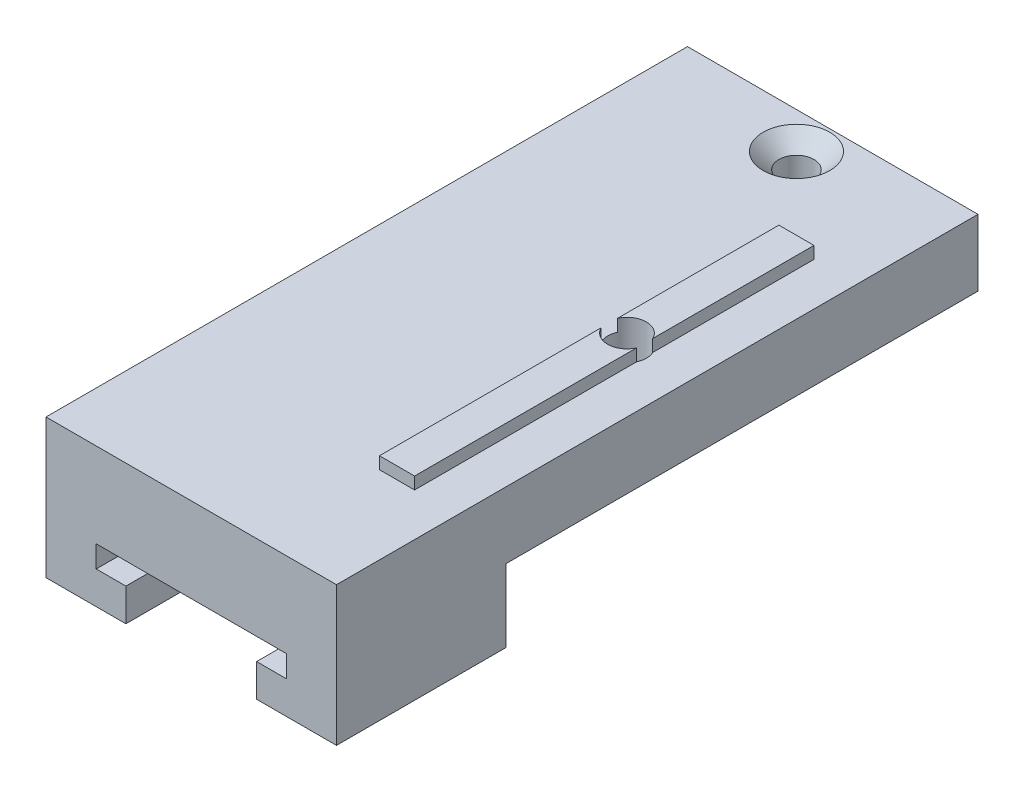
SolidWorks part; units mm, degrees
ref_plane "Front Plane" through (0, 0, 0) normal (0, 0, 1) x (1, 0, 0)
ref_plane "Top Plane" through (0, 0, 0) normal (0, 1, 0) x (1, 0, 0)
ref_plane "Right Plane" through (0, 0, 0) normal (1, 0, 0) x (0, 0, -1)
sketch "Sketch1" plane through (0, 0, 0) normal (0, 0, 1) x (1, 0, 0)
  line L0 (12, 0) -> (5.4, 0)
  line L1 (5.4, 0) -> (5.4, 2.7)
  line L2 (5.4, 2.7) -> (7.85, 2.7)
  line L3 (7.85, 2.7) -> (7.85, 4.5)
  line L5 (-5.4, 0) -> (-12, 0)
  line L6 (5.4, 0) -> (-5.4, 0) construction
  line L8 (7.85, 4.5) -> (-7.85, 4.5)
  line L9 (-7.85, 4.5) -> (-7.85, 2.7)
  line L10 (-7.85, 2.7) -> (-5.4, 2.7)
  line L11 (-5.4, 2.7) -> (-5.4, 0)
  line L13 (-12, 11.5) -> (12, 11.5)
  line L14 (-12, 11.5) -> (-12, 0)
  line L16 (12, 11.5) -> (12, 0)
  point P6 (0, 0)
  point P7 (5.4, 0)
  point P8 (0, 0)
  point P9 (0, 0)
  point P10 (5.3931, 0)
  dimension "D1" = 10.8
  dimension "D2" = 2.7
  dimension "D3" = 1.8
  dimension "D4" = 5.4
  dimension "D5" = 24
  dimension "D6" = 11.5
  dimension "D7" = 15.7
  dimension "D8" = 7
  dimension "D9" = 4.5
extrude "Main" add sketch "Sketch1" along normal blind 53
sketch "Sketch2" plane through (0, 0, 0) normal (0, 1, 0) x (1, 0, 0)
  line L0 (-12, -53) -> (-12, 0) construction
  line L1 (-12, 0) -> (12, 0)
  line L2 (-12, 0) -> (-12, -36)
  line L3 (-12, -36) -> (12, -36)
  line L4 (12, 0) -> (12, -36)
  line L5 (12, -53) -> (12, 0) construction
  line L6 (12, 0) -> (-12, 0) construction
  line L7 (-12, -53) -> (-5.4, -53) construction
  point P6 (10, 0)
  point P7 (12.0349, 0)
  point P8 (-10, 0)
  dimension "D1" = 17
extrude "Cut-Extrude1" cut sketch "Sketch2" along normal blind 6
sketch "Sketch3" plane through (0, 11.5, 0) normal (0, 1, 0) x (1, 0, 0)
  line L1 (8.45, -10) -> (5.55, -10)
  line L2 (8.45, -10) -> (8.45, -43)
  line L3 (8.45, -43) -> (5.55, -43)
  line L4 (5.55, -10) -> (5.55, -43)
  line L6 (12, -53) -> (12, 0) construction
  line L8 (12, 0) -> (-12, 0) construction
  line L9 (12, -53) -> (-12, -53) construction
  point P4 (6.45, -8.2228)
  point P6 (6.45, -34.8899)
  dimension "D1" = 2.9
  dimension "D2" = 3.55
  dimension "D3" = 10
  dimension "D4" = 10
extrude "MakerBeamRail" add sketch "Sketch3" along normal blind 1
sketch "Sketch4" plane through (0, 12.5, 0) normal (0, 1, 0) x (1, 0, 0)
  line L0 (12, -53) -> (12, 0) construction
  line L1 (12, 0) -> (-12, 0) construction
  circle A0 centre (7, -24) radius 1.6
  point P4 (12, -26.5)
  dimension "D1" = 3.2
  dimension "D2" = 5
  dimension "D3" = 24
extrude "MakerBeamHole" cut sketch "Sketch4" against normal through all
sketch "Sketch5" plane through (0, 6, 0) normal (0, -1, 0) x (-1, 0, 0)
  circle A0 centre (-7, -24) radius 4.35
  point P2 (-5, -24)
  dimension "D1" = 8.7
extrude "MakerBeamBigHole" cut sketch "Sketch5" against normal blind 3
sketch "Sketch6" plane through (0, 4.5, 0) normal (0, -1, 0) x (1, 0, 0)
  line L0 (7.85, 53) -> (-7.85, 53) construction
  line L1 (7.85, 36) -> (-7.85, 36)
  line L2 (7.85, 36) -> (7.85, 44.5)
  line L3 (7.85, 44.5) -> (-7.85, 44.5)
  line L4 (-7.85, 36) -> (-7.85, 44.5)
  point P5 (-7.5124, 34)
  point P6 (-7.8, 34)
  dimension "D1" = 8.5
extrude "PinHoles" cut sketch "Sketch6" against normal up to surface (1.5 mm away) up to face at (7, 6, 19.65)
hole_wizard "CSK for M2.5 Flat Head Machine Screw1" positions "Sketch8" profile "Sketch7" countersink size "M2.5" standard "ANSI Metric" end condition through all
sketch "Sketch8" plane through (0, 11.5, 0) normal (0, 1, 0) x (1, 0, 0)
  line L0 (12, 0) -> (-12, 0) construction
  line L1 (0, -6.875) -> (0, 6.875) construction
  point P0 (0, -3)
  dimension "D1" = 3
sketch "Sketch7" plane through (0, 11.5, 3) normal (1, 0, 0) x (0, 0, 1)
  line L0 (0, 0) -> (0, 11.5)
  line L1 (0, 11.5) -> (1.45, 11.5)
  line L2 (1.45, 11.5) -> (1.45, 1.3)
  line L3 (1.45, 1.3) -> (2.75, 0)
  line L5 (2.75, 0) -> (0, 0)
  line L6 (-1.45, 1.3) -> (-2.75, 0) construction
  line L11 (0, -6.35) -> (0, 107.95) construction
  dimension "Thru Hole Dia." = 2.9
  dimension "Thru Hole Depth" = 11.5
  dimension "Near C'Sink Dia." = 5.5
  dimension "Near C'Sink Angle" = 90
sketch "Sketch9" plane through (0, 0, 0) normal (0, -1, 0) x (-1, 0, 0)
  line L0 (-12, -53) -> (-12, -36) construction
  line L1 (-12, -39) -> (-5.4, -39)
  line L2 (-12, -39) -> (-12, -36)
  line L3 (-12, -36) -> (-5.4, -36)
  line L4 (-5.4, -39) -> (-5.4, -36)
  line L5 (-5.4, -53) -> (-5.4, -36) construction
  line L6 (-5.4, -53) -> (-12, -53) construction
  point P10 (-12, -31)
  dimension "D1" = 14
extrude "Cut-Extrude5" cut sketch "Sketch9" against normal up to surface (6 mm away) up to face at (0, 6, 4.45)
